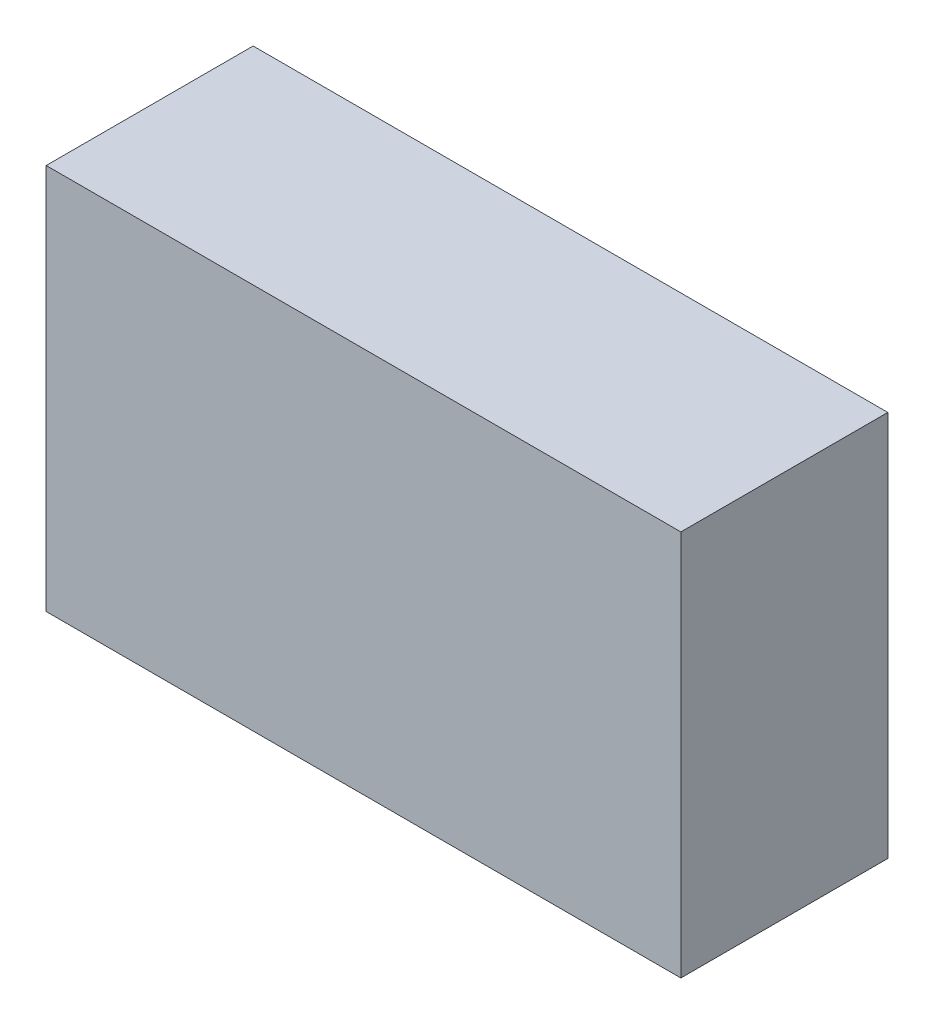
SolidWorks part; units mm, degrees
ref_plane "Front Plane" through (0, 0, 0) normal (0, 0, 1) x (1, 0, 0)
ref_plane "Top Plane" through (0, 0, 0) normal (0, 1, 0) x (1, 0, 0)
ref_plane "Right Plane" through (0, 0, 0) normal (1, 0, 0) x (0, 0, -1)
sketch "Sketch1" plane through (0, 0, 0) normal (0, 0, 1) x (1, 0, 0)
  line L1 (0, 0) -> (46, 0)
  line L2 (0, 0) -> (0, 28)
  line L3 (0, 28) -> (46, 28)
  line L4 (46, 0) -> (46, 28)
  dimension "D1" = 28
  dimension "D2" = 46
extrude "Boss-Extrude1" add sketch "Sketch1" along normal blind 15
